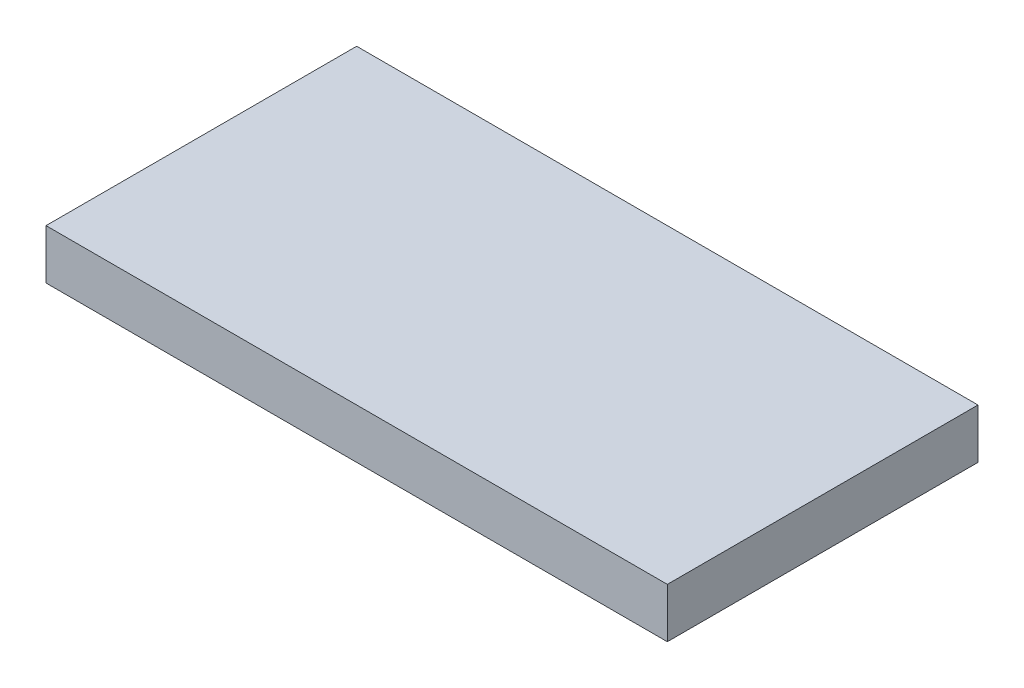
SolidWorks part; units mm, degrees
ref_plane "Front Plane" through (0, 0, 0) normal (0, 0, 1) x (1, 0, 0)
ref_plane "Top Plane" through (0, 0, 0) normal (0, 1, 0) x (1, 0, 0)
ref_plane "Right Plane" through (0, 0, 0) normal (1, 0, 0) x (0, 0, -1)
sketch "Sketch1" plane through (0, 0, 0) normal (0, 1, 0) x (1, 0, 0)
  line L1 (0, 0) -> (-25.4, 0)
  line L2 (0, 0) -> (0, 12.7)
  line L3 (0, 12.7) -> (-25.4, 12.7)
  line L4 (-25.4, 0) -> (-25.4, 12.7)
  dimension "D1" = 25.4
  dimension "D2" = 12.7
extrude "Boss-Extrude1" add sketch "Sketch1" along normal blind 2.032
